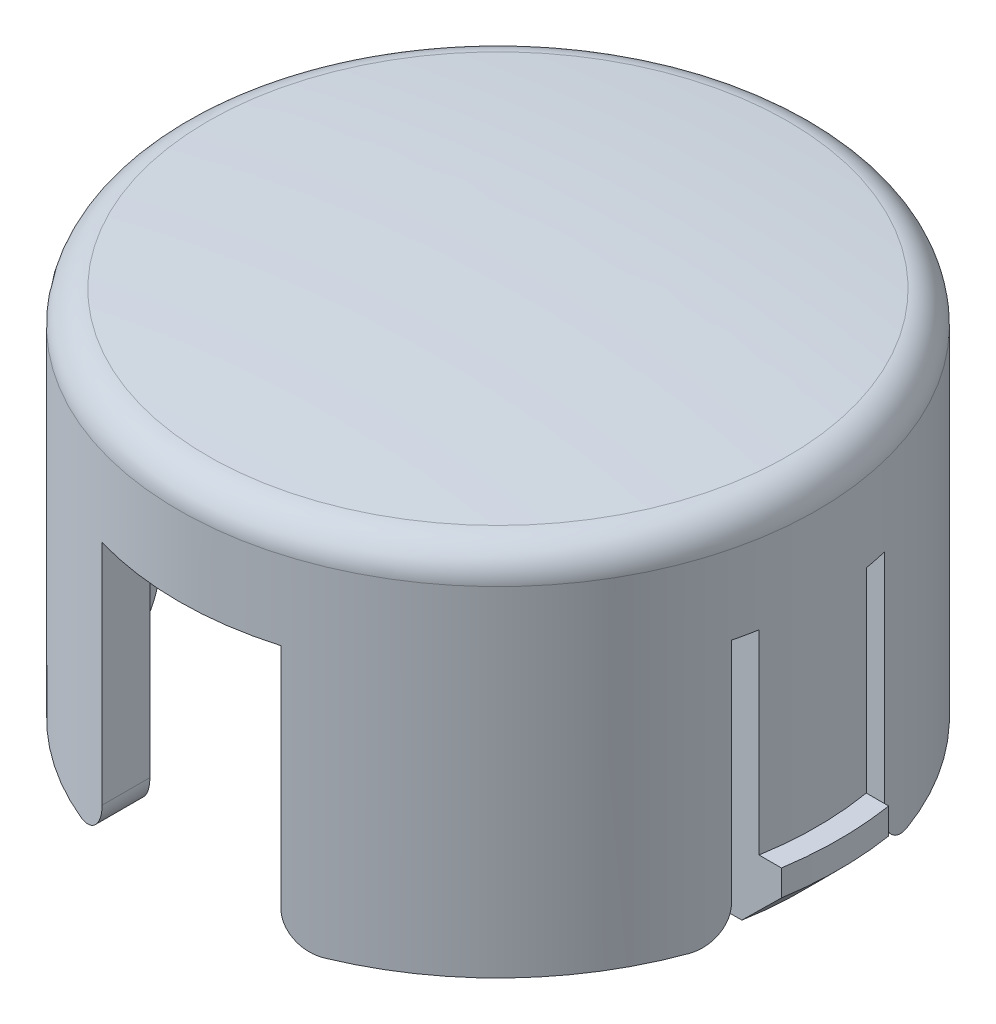
SolidWorks part; units mm, degrees
ref_plane "Front" through (0, 0, 0) normal (0, 0, 1) x (1, 0, 0)
ref_plane "Top" through (0, 0, 0) normal (0, 1, 0) x (1, 0, 0)
ref_plane "Right" through (0, 0, 0) normal (1, 0, 0) x (0, 0, -1)
sketch "Sketch1" plane through (0, 0, 0) normal (0, 0, 1) x (1, 0, 0)
  line L0 (0, 0) -> (0, 6.0399)
  line L1 (0, 6.0399) -> (21.0862, 6.0399) construction
  line L2 (0, 3.9609) -> (10.6934, 3.9609)
  line L3 (12.4714, 4.1956) -> (12.4714, -9.0477)
  line L4 (10.6934, 3.9609) -> (10.6934, -9.0477)
  line L5 (10.6934, -9.0477) -> (12.4714, -9.0477)
  arc A0 (0, 6.0399) -> (11.3313, 5.4589) centre (0, -104.7583) cw
  arc A1 (12.4714, 4.1956) -> (11.3313, 5.4589) centre (11.2014, 4.1956) ccw
  dimension "D1" = 1.27
  dimension "D2" = 12.4714
  dimension "D3" = 1.778
  dimension "D4" = 15.0876
revolve "dome/base" add sketch "Sketch1" angle 360 about L0
sketch "Sketch2" plane through (0, -9.0477, 0) normal (0, -1, 0) x (1, 0, 0)
  line L0 (-3.4925, 0) -> (3.4925, 0) construction
  line L1 (-3.4925, 16.1782) -> (3.4925, 16.1782)
  line L2 (-3.4925, 16.1782) -> (-3.4925, -16.1782)
  line L3 (-3.4925, -16.1782) -> (3.4925, -16.1782)
  line L4 (3.4925, 16.1782) -> (3.4925, -16.1782)
  line L5 (0, 2.0955) -> (0, 0) construction
  line L6 (-20.4861, 2.9845) -> (20.4861, 2.9845)
  line L7 (-20.4861, 2.9845) -> (-20.4861, 2.0955)
  line L8 (-20.4861, 2.0955) -> (20.4861, 2.0955)
  line L9 (20.4861, 2.9845) -> (20.4861, 2.0955)
  line L10 (-20.4861, -2.9845) -> (-20.4861, -2.0955)
  line L11 (-20.4861, -2.0955) -> (20.4861, -2.0955)
  line L12 (20.4861, -2.9845) -> (20.4861, -2.0955)
  line L13 (-20.4861, -2.9845) -> (20.4861, -2.9845)
  point P6 (0, 0)
  dimension "D1" = 6.985
  dimension "D2" = 0.889
  dimension "D3" = 5.969
extrude "cutout" cut sketch "Sketch2" against normal blind 10.16 contours L6 L9 L8 L7 | L11 L12 L13 L10 | L4 L3 L2 L1
sketch "Sketch3" plane through (0, -9.0477, 0) normal (0, -1, 0) x (1, 0, 0)
  line L0 (-12.2941, -2.0955) -> (-13.1693, -2.0955)
  line L1 (-12.2941, 2.0955) -> (-13.1693, 2.0955)
  line L2 (-12.2941, 2.0955) -> (-10.4861, 2.0955) construction
  line L3 (-12.2941, -2.0955) -> (-10.4861, -2.0955) construction
  line L4 (0, -13.335) -> (0, 13.335) construction
  line L5 (12.2941, 2.0955) -> (13.1693, 2.0955)
  line L6 (12.2941, -2.0955) -> (13.1693, -2.0955)
  circle A0 centre (0, 0) radius 13.335
  arc A1 (-12.2941, 2.0955) -> (-12.2941, -2.0955) centre (0, 0) ccw construction
  arc A2 (12.2941, -2.0955) -> (12.2941, 2.0955) centre (0, 0) ccw construction
  arc A3 (12.2941, -2.0955) -> (12.2941, 2.0955) centre (0, 0) ccw
  arc A4 (-12.2941, 2.0955) -> (-12.2941, -2.0955) centre (0, 0) ccw
  point P13 (-12.4714, 0)
  arc M2 (-12.2941, 2.0955) -> (-12.2941, -2.0955) centre (0, 0) ccw
  dimension "D1" = 26.67
extrude "tab" add sketch "Sketch3" against normal blind 2.54 contours L1 A0 L0 M2 | A3 L6 A0 L5
chamfer "tab chmf" distance 1.524 angle 45 2 edges at (13.335, -9.0477, 0) (-13.335, -9.0477, 0)
sketch "Sketch5" plane through (0, 3.9609, 0) normal (0, -1, 0) x (1, 0, 0)
  line L0 (0, 0.7184) -> (-7.912, -7.1936)
  line L1 (-7.1936, -7.912) -> (0, -0.7184)
  line L2 (0, 0) -> (0, -10.6934) construction
  line L3 (0, -0.7184) -> (0, 0.7184) construction
  line L4 (-7.912, 7.1936) -> (-0.7184, 0)
  line L5 (0.7184, 0) -> (-7.1936, 7.912)
  line L6 (7.1936, 7.912) -> (0, 0.7184)
  line L7 (0, -0.7184) -> (7.912, 7.1936)
  line L8 (7.912, -7.1936) -> (0.7184, 0)
  line L9 (-0.7184, 0) -> (7.1936, -7.912)
  circle A0 centre (0, 0) radius 10.6934 construction
  circle A1 centre (0, 0) radius 10.6934
  point P7 (0, 0)
  circle M1 centre (0, 0) radius 10.6934
  dimension "D1" = 1.016
  dimension "D3" = 45
extrude "cross" add sketch "Sketch5" along normal blind 7.62 contours L9 L0 L1 M1 | L7 L9 L8 M1 | L5 L7 L6 M1 | L0 L9 L7 L5 | L0 L5 L4 M1
sketch "Sketch4" plane through (0, 3.9609, 0) normal (0, -1, 0) x (1, 0, 0)
  line L0 (-1.651, 0) -> (1.651, 0) construction
  line L1 (-1.651, -3.8481) -> (1.651, -3.8481)
  line L2 (-1.651, -3.8481) -> (-1.651, 3.8481)
  line L3 (-1.651, 3.8481) -> (1.651, 3.8481)
  line L4 (1.651, -3.8481) -> (1.651, 3.8481)
  point P6 (0, 0)
  dimension "D1" = 3.302
  dimension "D2" = 7.6962
extrude "box" add sketch "Sketch4" along normal offset from surface (13.0594 mm away) 0.0508 up to face at (-7.8578, -9.0477, -7.5064) offset beyond the face yes
sketch "Sketch6" plane through (0, -9.0985, 0) normal (0, -1, 0) x (1, 0, 0)
  line L8 (0.889, 3.0861) -> (-0.889, 3.0861)
  line L9 (-0.889, 3.0861) -> (-0.889, -3.0861)
  line L10 (-0.889, -3.0861) -> (0.889, -3.0861)
  line L11 (0.889, -3.0861) -> (0.889, 3.0861)
  line L12 (0.889, 3.0861) -> (-0.889, 3.0861)
  line L13 (-0.889, 3.0861) -> (-0.889, -3.0861)
  line L14 (-0.889, -3.0861) -> (0.889, -3.0861)
  line L15 (0.889, -3.0861) -> (0.889, 3.0861)
  dimension "D1" = 0.762
extrude "boxcut" cut sketch "Sketch6" against normal up to surface (13.0594 mm away) up to face at (0, 3.9609, -5.1734)
fillet "Fillet1" radius 1.27 8 edges at (3.4925, -9.0477, 11.0397) (3.4925, -9.0477, -11.0397) (-3.4925, -9.0477, 11.0397) (-3.4925, -9.0477, -11.0397) (-11.1888, -9.0477, -2.9845) (11.1888, -9.0477, -2.9845) (11.1888, -9.0477, 2.9845) (-11.1888, -9.0477, 2.9845)
